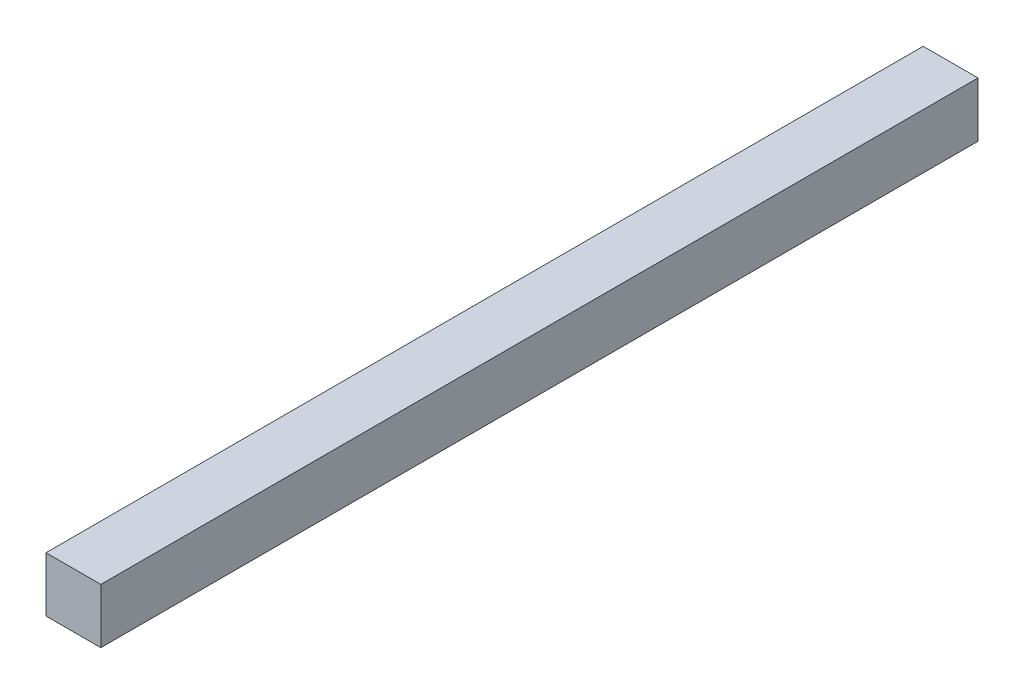
SolidWorks part; units mm, degrees
ref_plane "Front Plane" through (0, 0, 0) normal (0, 0, 1) x (1, 0, 0)
ref_plane "Top Plane" through (0, 0, 0) normal (0, 1, 0) x (1, 0, 0)
ref_plane "Right Plane" through (0, 0, 0) normal (1, 0, 0) x (0, 0, -1)
sketch "Sketch1" plane through (0, 0, 0) normal (0, 0, 1) x (1, 0, 0)
  line L1 (-65.7704, 30.2369) -> (-55.7704, 30.2369)
  line L2 (-65.7704, 30.2369) -> (-65.7704, 20.2369)
  line L3 (-65.7704, 20.2369) -> (-55.7704, 20.2369)
  line L4 (-55.7704, 30.2369) -> (-55.7704, 20.2369)
extrude "Boss-Extrude1" add sketch "Sketch1" along normal blind 160
